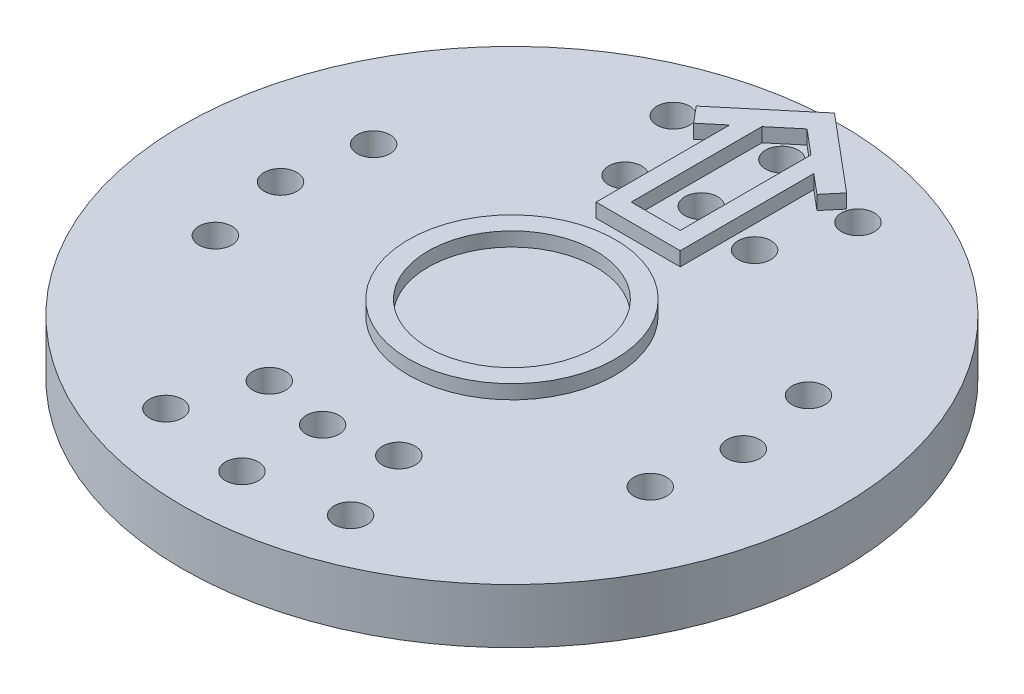
SolidWorks part; units mm, degrees
ref_plane "Front Plane" through (0, 0, 0) normal (0, 0, 1) x (1, 0, 0)
ref_plane "Top Plane" through (0, 0, 0) normal (0, 1, 0) x (1, 0, 0)
ref_plane "Right Plane" through (0, 0, 0) normal (1, 0, 0) x (0, 0, -1)
sketch "Sketch1" plane through (0, 0, 0) normal (0, 1, 0) x (1, 0, 0)
  circle A0 centre (0, 0) radius 11.938
  dimension "D1" = 23.876
extrude "Extrude1" add sketch "Sketch1" against normal blind 1.9812
sketch "Sketch2" plane through (0, -1.9812, 0) normal (0, -1, 0) x (1, 0, 0)
  circle A0 centre (0, 0) radius 4.445
  dimension "D1" = 8.89
extrude "Extrude2" add sketch "Sketch2" along normal blind 2.286
hole_wizard "3/64 (0.04688) Diameter Hole1" positions "3DSketch1" profile "Sketch4" hole size "3/64" standard "Ansi Inch" end condition through all
sketch3d "3DSketch1"
  line L0 (0, 0, 0) -> (-3.3446, 0, -9.1893) construction
  line L2 (0, 0, 0) -> (3.3446, 0, -9.1893) construction
  line L4 (0, 0, 0) -> (-7.8765, 0, -2.8668) construction
  line L8 (-8.382, 0, 0) -> (0, 0, 0) construction
  line L10 (-7.8765, 0, 2.8668) -> (0, 0, 0) construction
  line L12 (0, 0, 0) -> (0, 0, -9.779) construction
  circle A0 centre (0, 0, 0) radius 6.858 construction
  circle A1 centre (0, 0, 0) radius 9.779 construction
  circle A2 centre (0, 0, 0) radius 8.382 construction
  point P0 (0, 0, -6.858)
  point P2 (-2.3456, 0, -6.4444)
  point P4 (2.3456, 0, -6.4444)
  point P6 (3.3446, 0, -9.1893)
  point P8 (0, 0, -9.779)
  point P10 (-3.3446, 0, -9.1893)
  point P12 (-7.8765, 0, -2.8668)
  point P14 (-8.382, 0, 0)
  point P16 (-7.8765, 0, 2.8668)
  point P27 (0, -6.858, 0)
  point P40 (0, 9.779, 0)
  point P89 (0, -8.382, 0)
  dimension "D1" = 13.716
  dimension "D3" = 19.558
  dimension "D5" = 16.764
  dimension "D2" = 20
  dimension "D4" = 6.6892
sketch "Sketch4" plane through (0, 0, -6.858) normal (1, 0, 0) x (0, 0, 1)
  line L0 (0, 0) -> (0, 4.2672)
  line L1 (0, 4.2672) -> (0.5954, 4.2672)
  line L2 (0.5954, 4.2672) -> (0.5954, 0)
  line L5 (0.5954, 0) -> (0, 0)
  line L11 (0, -6.35) -> (0, 107.95) construction
  dimension "Thru Hole Dia." = 1.1908
  dimension "Thru Hole Depth" = 4.2672
pattern_circular "CirPattern1" count 2 over 360 about axis through (0, 0, 0) along (0, 1, 0) of "3/64 (0.04688) Diameter Hole1"
sketch "Sketch6" plane through (0, 0, 0) normal (0, 1, 0) x (1, 0, 0)
  circle A0 centre (0, 0) radius 3.7465
  circle A1 centre (0, 0) radius 3.0353
  dimension "D1" = 0.7112
  dimension "D2" = 7.493
extrude "Extrude4" add sketch "Sketch6" along normal blind 0.508
sketch "Sketch5" plane through (0, 0, 0) normal (0, 1, 0) x (1, 0, 0)
  line L0 (-2.7241, 9.3982) -> (0, 11.684)
  line L1 (0, 11.684) -> (2.7241, 9.3982)
  line L2 (2.7241, 9.3982) -> (2.2342, 8.8145)
  line L3 (2.2342, 8.8145) -> (1.524, 9.4105)
  line L4 (0, 10.6893) -> (-0.889, 9.9433)
  line L5 (-2.2342, 8.8145) -> (-2.7241, 9.3982)
  line L6 (0, 10.6893) -> (0, 11.684) construction
  line L7 (-1.524, 9.4105) -> (-1.524, 4.572)
  line L8 (-1.524, 4.572) -> (1.524, 4.572)
  line L9 (1.524, 4.572) -> (1.524, 9.4105)
  line L10 (-0.889, 9.9433) -> (-0.889, 5.207)
  line L11 (-0.889, 5.207) -> (0.889, 5.207)
  line L12 (0.889, 5.207) -> (0.889, 9.9433)
  line L13 (-1.524, 9.4105) -> (-2.2342, 8.8145)
  line L14 (0.889, 9.9433) -> (0, 10.6893)
  circle A0 centre (0, 0) radius 11.938 construction
  dimension "D1" = 100
  dimension "D2" = 3.556
  dimension "D3" = 0.762
  dimension "D4" = 0.635
  dimension "D5" = 11.684
  dimension "D6" = 4.572
  dimension "D7" = 0.635
  dimension "D8" = 3.048
extrude "Extrude3" add sketch "Sketch5" along normal blind 0.508
